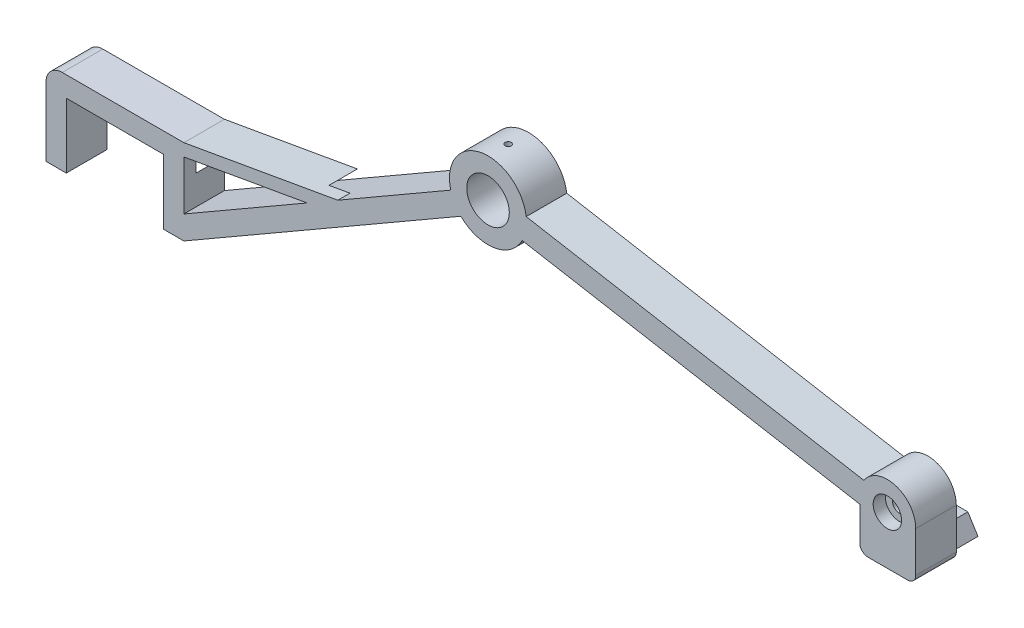
SolidWorks part; units mm, degrees
material "ABS"
ref_plane "Přední rovina" through (0, 0, 0) normal (0, 0, 1) x (1, 0, 0)
ref_plane "Horní rovina" through (0, 0, 0) normal (0, 1, 0) x (1, 0, 0)
ref_plane "Pravá rovina" through (0, 0, 0) normal (1, 0, 0) x (0, 0, -1)
sketch "Skica1" plane through (0, 0, 0) normal (0, 0, 1) x (1, 0, 0)
  line L0 (0, 0) -> (0, 16)
  line L1 (0, 16) -> (24, 16)
  line L2 (24, 16) -> (24, 0)
  line L3 (24, 0) -> (29, 0)
  line L4 (29, 0) -> (97.3127, 39.4404)
  line L5 (0, 0) -> (-5, 0)
  line L6 (-5, 0) -> (-5, 21)
  line L7 (-5, 21) -> (29, 21)
  line L8 (29, 21) -> (29, 5.7735)
  line L9 (29, 5.7735) -> (94.8127, 43.7705)
  line L10 (104, 49.0748) -> (104, 43.3013) construction
  line L11 (113.4206, 47.4137) -> (196.6749, 32.7337)
  line L12 (104, 46.188) -> (202.4808, 28.8232) construction
  line L13 (195.6876, 27.1343) -> (112.4333, 41.8143)
  line L14 (94.8127, 43.7705) -> (104, 49.0748) construction
  line L15 (104, 49.0748) -> (104, 43.3013) construction
  line L16 (104, 43.3013) -> (97.3127, 39.4404) construction
  line L18 (112.4333, 41.8143) -> (104, 43.3013) construction
  line L20 (113.4206, 47.4137) -> (104, 49.0748) construction
  arc A0 (97.3127, 39.4404) -> (112.4333, 41.8143) centre (104, 46.188) ccw
  arc A1 (113.4206, 47.4137) -> (94.8127, 43.7705) centre (104, 46.188) ccw
  circle A2 centre (104, 46.188) radius 5.25
  arc A3 (195.6876, 27.1343) -> (196.6749, 32.7337) centre (202.4808, 28.8232) ccw
  dimension "D11" = 19
  dimension "D12" = 10.5
  dimension "D14" = 7
  dimension "D1" = 5
  dimension "D2" = 5
  dimension "D3" = 24
  dimension "D4" = 16
  dimension "D5" = 5
  dimension "D6" = 5
  dimension "D7" = 5
  dimension "D8" = 80
  dimension "D9" = 60
  dimension "D10" = 140
  dimension "D13" = 100
extrude "Přidat vysunutím1" add sketch "Skica1" along normal mid plane 10
fillet "Zaoblit1" radius 4 1 edges at (-5, 21, 0)
sketch "Skica2" plane through (0, 0, 5) normal (0, 0, 1) x (1, 0, 0)
  circle A0 centre (202.4808, 28.8232) radius 1.75
  dimension "D1" = 3.5
sketch "Skica4" plane through (0, 0, 0) normal (0, 0, 1) x (1, 0, 0)
  line L0 (29, 21) -> (66.9691, 27.695)
  line L1 (94.8127, 43.7705) -> (29, 5.7735) construction
  line L2 (66.9691, 27.695) -> (59.3728, 23.3093)
  line L3 (59.3728, 23.3093) -> (29, 17.9537)
  line L4 (29, 5.7735) -> (29, 21) construction
  line L5 (29, 17.9537) -> (29, 21)
  dimension "D1" = 3
  dimension "D2" = 80
extrude "Přidat vysunutím3" add sketch "Skica4" along normal mid plane 10
sketch "Skica5" plane through (0, 0, 5) normal (0, 0, 1) x (1, 0, 0)
  circle A0 centre (202.4808, 28.8232) radius 1.75
  circle A1 centre (202.4808, 28.8232) radius 4.25
  dimension "D1" = 2.5
  dimension "D2" = 3.5
extrude "Přidat vysunutím4" add sketch "Skica5" along normal blind 1
sketch "Skica8" plane through (0, 0, 0) normal (0, -1, 0) x (1, 0, 0)
  line L0 (-1.5, 0) -> (25.5, 0) construction
  line L1 (12, 5) -> (12, -6.4114) construction
  line L2 (0, 5) -> (24, 5) construction
  circle A0 centre (-1.5, 0) radius 1.05
  circle A1 centre (25.5, 0) radius 1.05
  dimension "D3" = 2.1
  dimension "D1" = 27
  dimension "D2" = 13.5
extrude "Odebrat vysunutím3" cut sketch "Skica8" against normal blind 6
sketch "Skica9" plane through (0, 0, 5) normal (0, 0, 1) x (1, 0, 0)
  line L0 (24, 16) -> (29, 16)
  line L1 (29, 5.7735) -> (29, 17.9537) construction
  line L2 (29, 16) -> (29, 13)
  line L3 (29, 13) -> (24, 8)
  line L4 (24, 16) -> (24, 0) construction
  line L5 (24, 8) -> (24, 16)
  dimension "D1" = 45
  dimension "D2" = 3
extrude "Odebrat vysunutím4" cut sketch "Skica9" against normal blind 7
extrude "Odebrat vysunutím5" cut sketch "Skica2" against normal blind 10
sketch "Skica10" plane through (0, 0, -5) normal (0, 0, -1) x (-1, 0, 0)
  circle A0 centre (-202.4808, 28.8232) radius 3.5
  dimension "D1" = 7
extrude "Odebrat vysunutím6" cut sketch "Skica10" against normal blind 3
mirror "Zrcadlit1" of bodies 114
delete or keep bodies "Tělo-Odstranit1" type delete bodies bodies 114
sketch "Skica11" plane through (0, 0, 0) normal (0, 1, 0) x (1, 0, 0)
  line L1 (113.4206, 15) -> (94.5, 15) construction
  line L2 (94.5, 15) -> (94.5, 5) construction
  line L3 (94.5, 10) -> (103.9603, 10) construction
  line L4 (103.9603, 10) -> (103.9603, 15) construction
  circle A0 centre (103.9603, 10) radius 0.75
  dimension "D1" = 1.5
extrude "Odebrat vysunutím7" cut sketch "Skica11" along normal blind 10 from offset 50
sketch "Skica12" plane through (0, 0, -15) normal (0, 0, -1) x (-1, 0, 0)
  line L2 (-209.4808, 28.8232) -> (-209.4808, 16.8232)
  line L3 (-209.4808, 16.8232) -> (-195.6876, 16.8232)
  line L4 (-195.6876, 27.1343) -> (-195.6876, 16.8232)
  arc A1 (-196.6749, 32.7337) -> (-195.6876, 27.1343) centre (-202.4808, 28.8232) ccw construction
  arc A2 (-209.4808, 28.8232) -> (-195.6876, 27.1343) centre (-202.4808, 28.8232) ccw
  dimension "D1" = 12
extrude "Přidat vysunutím5" add sketch "Skica12" against normal up to surface (10 mm away)
sketch "Skica13" plane through (0, 0, -15) normal (0, 0, -1) x (-1, 0, 0)
  line L0 (-202.5842, 16.8232) -> (-202.5842, 19.6565) construction
  line L1 (-209.4808, 16.8232) -> (-195.6876, 16.8232) construction
  line L3 (-204.3342, 20.8232) -> (-200.8342, 20.8232)
  line L4 (-204.3342, 20.8232) -> (-206.8342, 16.8232)
  line L5 (-206.8342, 16.8232) -> (-198.3342, 16.8232)
  line L6 (-200.8342, 20.8232) -> (-198.3342, 16.8232)
  line L7 (-204.3342, 20.8232) -> (-198.3342, 16.8232) construction
  line L8 (-206.8342, 16.8232) -> (-200.8342, 20.8232) construction
  dimension "D1" = 4
  dimension "D2" = 8.5
  dimension "D3" = 3.5
extrude "Přidat vysunutím6" add sketch "Skica13" along normal blind 8
fillet "Zaoblit2" radius 2 2 edges at (195.6876, 16.8232, -10) (209.4808, 16.8232, -10)
sketch "Skica14" plane through (0, 0, -15) normal (0, 0, -1) x (-1, 0, 0)
  line L0 (-59.3728, 23.3093) -> (-66.9691, 27.695)
  line L1 (-66.9691, 27.695) -> (-61.7862, 26.7811)
  line L2 (-66.9691, 27.695) -> (-29, 21) construction
  line L3 (-61.7862, 26.7811) -> (-54.1899, 22.3954)
  line L4 (-29, 17.9537) -> (-59.3728, 23.3093) construction
  line L5 (-54.1899, 22.3954) -> (-59.3728, 23.3093)
  dimension "D1" = 1.8
extrude "Odebrat vysunutím8" cut sketch "Skica14" against normal up to surface (7 mm away) up to face at (26.5, 13.25, -8)
equation "\"D2@Skica8\"=\"D1@Skica8\"/2"
